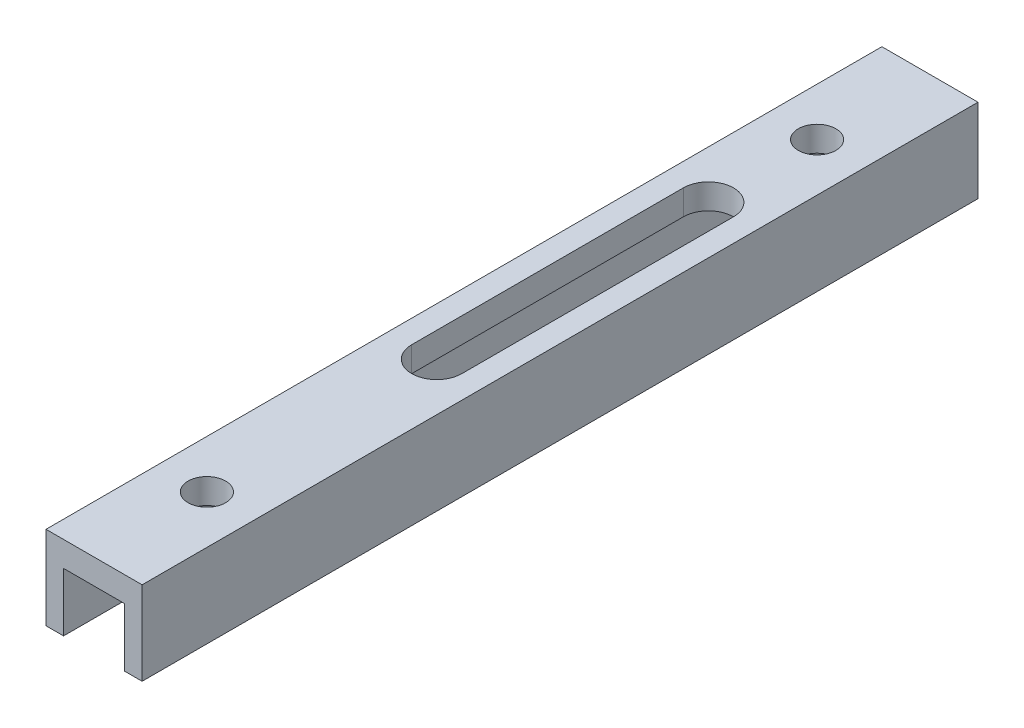
SolidWorks part; units mm, degrees
ref_plane "Plan de face" through (0, 0, 0) normal (0, 0, 1) x (1, 0, 0)
ref_plane "Plan de dessus" through (0, 0, 0) normal (0, 1, 0) x (1, 0, 0)
ref_plane "Plan de droite" through (0, 0, 0) normal (1, 0, 0) x (0, 0, -1)
sketch "Esquisse1" plane through (0, 0, 0) normal (0, 0, 1) x (1, 0, 0)
  line L0 (-5.75, 0) -> (5.75, 0)
  line L1 (5.75, 0) -> (5.75, -10)
  line L2 (5.75, -10) -> (3.65, -10)
  line L3 (3.65, -10) -> (3.65, -3)
  line L4 (3.65, -3) -> (-3.65, -3)
  line L5 (-3.65, -3) -> (-3.65, -10)
  line L6 (-3.65, -10) -> (-5.75, -10)
  line L7 (-5.75, -10) -> (-5.75, 0)
  line L8 (-3.65, -10) -> (3.65, -10) construction
  line L9 (0, -3) -> (0, 0) construction
  dimension "D1" = 11.5
  dimension "D2" = 7.3
  dimension "D3" = 7
  dimension "D4" = 10
extrude "Boss.-Extru.1" add sketch "Esquisse1" against normal blind 100
sketch "Esquisse2" plane through (0, 0, 0) normal (0, 1, 0) x (1, 0, 0)
  line L0 (0, 0) -> (0, 100) construction
  line L1 (5.75, 100) -> (-5.75, 100) construction
  line L2 (5.75, 0) -> (-5.75, 0) construction
  line L5 (-3, 73.5) -> (-3, 41)
  line L7 (3, 73.5) -> (3, 41)
  circle A0 centre (0, 86.5) radius 2.25
  circle A1 centre (0, 13.5) radius 2.25
  arc A2 (-3, 73.5) -> (3, 73.5) centre (0, 73.5) cw
  arc A3 (3, 41) -> (-3, 41) centre (0, 41) cw
  dimension "D1" = 4.5
  dimension "D2" = 73
  dimension "D3" = 13.5
  dimension "D4" = 6
  dimension "D5" = 13
  dimension "D18" = 27.5
  dimension "D19" = 32.5
extrude "Enlèv. mat.-Extru.1" cut sketch "Esquisse2" against normal through all
